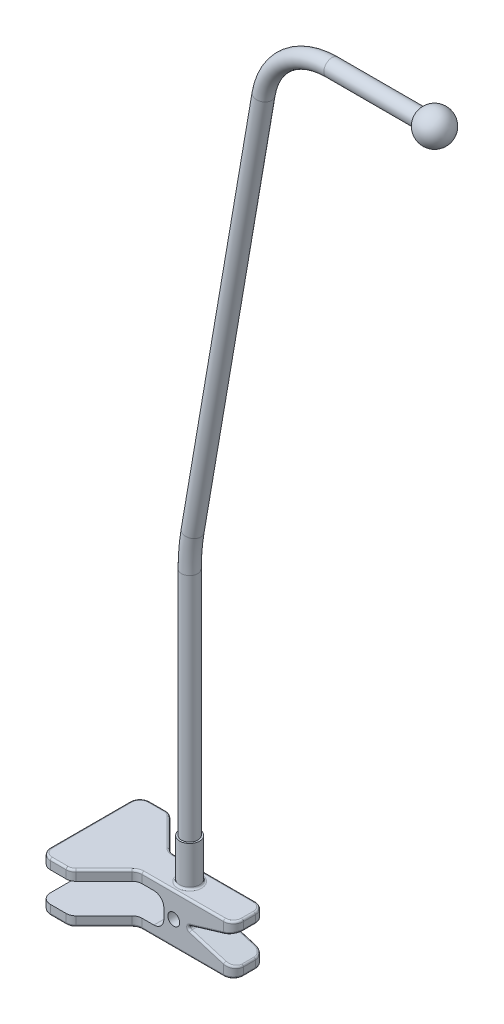
SolidWorks part; units mm, degrees
ref_plane "Alzado" through (0, 0, 0) normal (0, 0, 1) x (1, 0, 0)
ref_plane "Planta" through (0, 0, 0) normal (0, 1, 0) x (1, 0, 0)
ref_plane "Vista lateral" through (0, 0, 0) normal (1, 0, 0) x (0, 0, -1)
sketch "Croquis1" plane through (0, 0, 0) normal (0, 1, 0) x (1, 0, 0)
  circle A0 centre (0, 0) radius 5
  dimension "D1" = 10
extrude "Saliente-Extruir1" add sketch "Croquis1" along normal blind 20
sketch "Croquis2" plane through (0, 0, 0) normal (0, 0, 1) x (1, 0, 0)
  line L0 (30, 0) -> (-50, 0)
  line L1 (-50, 0) -> (-50, -5)
  line L2 (-50, -5) -> (-5, -5)
  line L6 (30, -25) -> (-50, -25)
  line L7 (-50, -25) -> (-50, -20)
  line L8 (-50, -20) -> (-5, -20)
  line L9 (-5, -20) -> (-5, -5)
  line L10 (5, -12.5) -> (-5, -12.5) construction
  line L11 (30, 0) -> (30, -5)
  line L12 (30, -5) -> (5, -12.5)
  line L13 (5, -12.5) -> (30, -20)
  line L14 (30, -20) -> (30, -25)
  line L15 (0, -12.5) -> (0, 0) construction
  dimension "D1" = 30
  dimension "D2" = 50
  dimension "D3" = 5
  dimension "D4" = 10
  dimension "D5" = 15
extrude "Saliente-Extruir2" add sketch "Croquis2" along normal mid plane 50
sketch "Croquis3" plane through (0, 0, 0) normal (0, 1, 0) x (1, 0, 0)
  line L0 (0, 0) -> (-50, 0) construction
  line L1 (-50, -25) -> (-50, 25) construction
  line L2 (-35, -25) -> (-18, -8)
  line L3 (30, -25) -> (-50, -25) construction
  line L4 (-18, -8) -> (30, -8)
  line L5 (30, -25) -> (30, 25) construction
  line L6 (30, -8) -> (30, -25)
  line L7 (30, -25) -> (-35, -25)
  line L8 (30, 8) -> (30, 25)
  line L9 (-18, 8) -> (30, 8)
  line L10 (-35, 25) -> (-18, 8)
  line L11 (30, 25) -> (-35, 25)
  dimension "D1" = 15
  dimension "D2" = 16
  dimension "D3" = 45
extrude "Cortar-Extruir1" cut sketch "Croquis3" against normal through all
sketch "Croquis4" plane through (0, 20, 0) normal (0, 1, 0) x (1, 0, 0)
  circle A1 centre (0, 0) radius 4.125
  dimension "D1" = 8.25
sketch "Croquis5" plane through (0, 0, 0) normal (0, 0, 1) x (1, 0, 0)
  line L0 (0, 20) -> (0, 135.9386)
  line L2 (1.4728, 153.2404) -> (37.1057, 361.0192)
  line L3 (71.4796, 390) -> (123, 390)
  line L4 (4.125, 20) -> (-4.125, 20) construction
  arc A0 (0, 135.9386) -> (1.4728, 153.2404) centre (102.3619, 135.9386) cw
  arc A1 (37.1057, 361.0192) -> (71.4796, 390) centre (71.4796, 355.1242) cw
  point P2 (73.5901, 390)
  point P12 (37.1057, 361.0192)
  dimension "D2" = 370
  dimension "D3" = 123
fillet "Redondeo1" radius 5 18 edges at (-18, -22.5, 8) (-18, -2.5, 8) (-18, -22.5, -8) (-18, -2.5, -8) (-35, -22.5, -25) (-35, -2.5, -25) (-50, -22.5, -25) (30, -2.5, -8) (30, -2.5, 8) (30, -22.5, -8) (30, -22.5, 8) (-50, -22.5, 25) (-35, -22.5, 25) (-35, -2.5, 25) (-50, -2.5, -25) (-50, -2.5, 25) (-5, -20, 0) (-5, -5, 0)
fillet "Redondeo2" radius 1 44 edges at (-48.5355, -25, -23.5355) (-50, -25, 0) (-48.5355, -25, 23.5355) (-41.0355, -25, 25) (-35.1577, -25, 24.6194) (-26.5, -25, 16.5) (-17.8423, -25, 8.3806) (4.5355, -25, 8) (28.5355, -25, 6.5355) (30, -25, 0) (28.5355, -25, -6.5355) (4.5355, -25, -8) (-17.8423, -25, -8.3806) (-26.5, -25, -16.5) (-35.1577, -25, -24.6194) (-41.0355, -25, -25) (-17.8423, 0, -8.3806) (4.5355, 0, -8) (28.5355, 0, -6.5355) (30, 0, 0) (28.5355, 0, 6.5355) (4.5355, 0, 8) (-17.8423, 0, 8.3806) (-26.5, 0, 16.5) (-35.1577, 0, 24.6194) (-41.0355, 0, 25) (-48.5355, 0, 23.5355) (-50, 0, 0) (-48.5355, 0, -23.5355) (-41.0355, 0, -25) (-35.1577, 0, -24.6194) (-26.5, 0, -16.5) (0, 0, 5) (5, -12.5, 0) (30, -5, 0) (28.5355, -5.4393, 6.5355) (28.5355, -5.4393, -6.5355) (15, -9.5, 8) (15, -9.5, -8) (28.5355, -19.5607, 6.5355) (15, -15.5, 8) (15, -15.5, -8) (28.5355, -19.5607, -6.5355) (30, -20, 0)
sweep "Barrer1" add profiles "Croquis4" path "Croquis5"
sketch "Croquis6" plane through (0, 0, 0) normal (0, 0, 1) x (1, 0, 0)
  line L0 (123, 390) -> (123, 381.75)
  line L1 (123, 398.25) -> (123, 390)
  arc A0 (123, 381.75) -> (123, 398.25) centre (123, 390) ccw
  dimension "D1" = 8.25
revolve "Revolución1" add sketch "Croquis6" angle 360 about L1
sketch "Croquis7" plane through (0, 0, 8) normal (0, 0, 1) x (1, 0, 0)
  line L0 (0, 0) -> (0, -12.5) construction
  line L1 (0, -12.5) -> (-5, -12.5) construction
  line L2 (-5, -15) -> (-5, -10) construction
  circle A0 centre (0, -12.5) radius 3
  dimension "D1" = 6
extrude "Cortar-Extruir2" cut sketch "Croquis7" against normal through all
